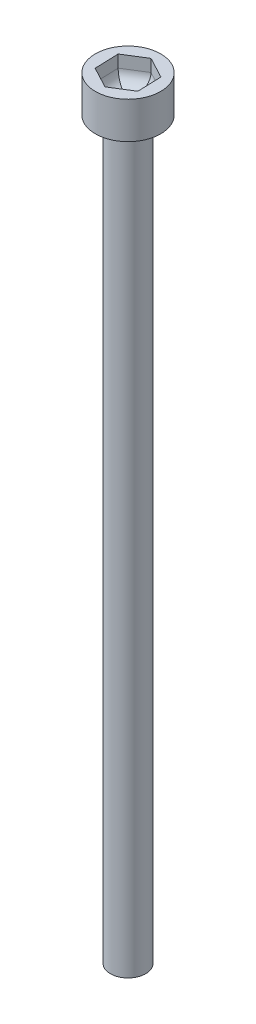
SolidWorks part; units mm, degrees
ref_plane "Front Plane" through (0, 0, 0) normal (0, 0, 1) x (1, 0, 0)
ref_plane "Top Plane" through (0, 0, 0) normal (0, 1, 0) x (1, 0, 0)
ref_plane "Right Plane" through (0, 0, 0) normal (1, 0, 0) x (0, 0, -1)
sketch "Sketch1" plane through (0, 0, 0) normal (0, 0, 1) x (1, 0, 0)
  line L0 (0, 0) -> (1.44, 0)
  line L1 (0, 0) -> (0, 63)
  line L2 (0, 63) -> (2.665, 63)
  line L3 (2.665, 63) -> (2.665, 60)
  line L4 (2.665, 60) -> (1.44, 60)
  line L5 (1.44, 60) -> (1.44, 0)
  line L6 (0, 63) -> (0, 0) construction
  line L7 (0, 0) -> (1.44, 0) construction
  dimension "D1" = 60
  dimension "D2" = 3
  dimension "D3" = 2.665
  dimension "D4" = 1.44
revolve "Revolve2" add sketch "Sketch1" angle 360 about L1
cosmetic thread "Cosmetic Thread2" parameters "D1"=20, "D2"=1.993
sketch "Sketch3" plane through (0, 63, 0) normal (0, 1, 0) x (1, 0, 0)
  line L1 (1.72, -0.9146) -> (1.6521, 1.0323)
  line L2 (1.6521, 1.0323) -> (-0.0679, 1.9469)
  line L3 (-0.0679, 1.9469) -> (-1.72, 0.9146)
  line L4 (-1.72, 0.9146) -> (-1.6521, -1.0323)
  line L5 (-1.6521, -1.0323) -> (0.0679, -1.9469)
  line L6 (0.0679, -1.9469) -> (1.72, -0.9146)
  circle A0 centre (0, 0) radius 1.6871 construction
extrude "Cut-Extrude1" cut sketch "Sketch3" against normal blind 2
fillet "Fillet1" radius 1 6 edges at (0.894, 61, 1.4308) (-0.7921, 61, 1.4896) (-1.6861, 61, 0.0588) (1.6861, 61, -0.0588) (0.7921, 61, -1.4896) (-0.894, 61, -1.4308)
